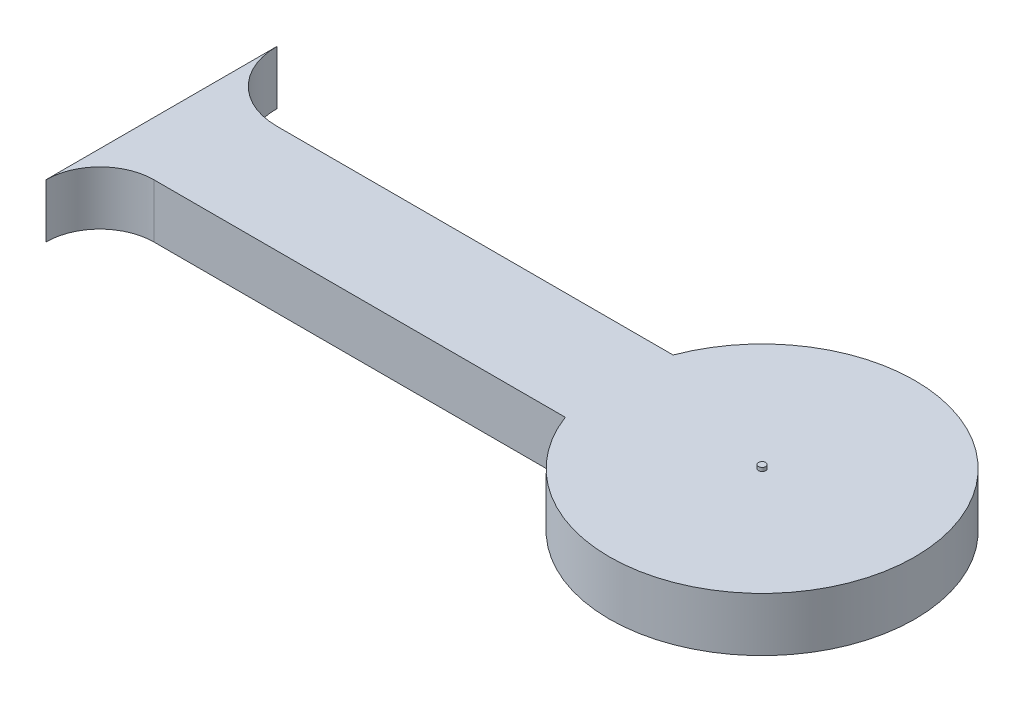
SolidWorks part; units mm, degrees
ref_plane "Plano frontal" through (0, 0, 0) normal (0, 0, 1) x (1, 0, 0)
ref_plane "Plano superior" through (0, 0, 0) normal (0, 1, 0) x (1, 0, 0)
ref_plane "Plano direito" through (0, 0, 0) normal (1, 0, 0) x (0, 0, -1)
sketch "Esboço1" plane through (0, 0, 0) normal (0, 1, 0) x (1, 0, 0)
  line L0 (-3.9765, 1.5) -> (-15, 1.5)
  line L1 (-3.9765, -1.5) -> (-15.4217, -1.5)
  line L2 (-16.9217, 3.4217) -> (-16.9217, -3)
  arc A0 (-3.9765, -1.5) -> (-3.9765, 1.5) centre (0, 0) ccw
  arc A1 (-16.9217, 3.4217) -> (-15, 1.5) centre (-15, 3.4217) ccw
  arc A2 (-15.4217, -1.5) -> (-16.9217, -3) centre (-15.4217, -3) ccw
  dimension "D1" = 15
  dimension "D2" = 8.5
  dimension "D3" = 3
  dimension "D4" = 1.5
extrude "Ressalto-extrusão1" add sketch "Esboço1" along normal blind 1.5
sketch "Esboço2" plane through (0, 1.5, 0) normal (0, 1, 0) x (1, 0, 0)
  circle A0 centre (0, 0) radius 0.1
extrude "Ressalto-extrusão2" add sketch "Esboço2" along normal blind 0.1
